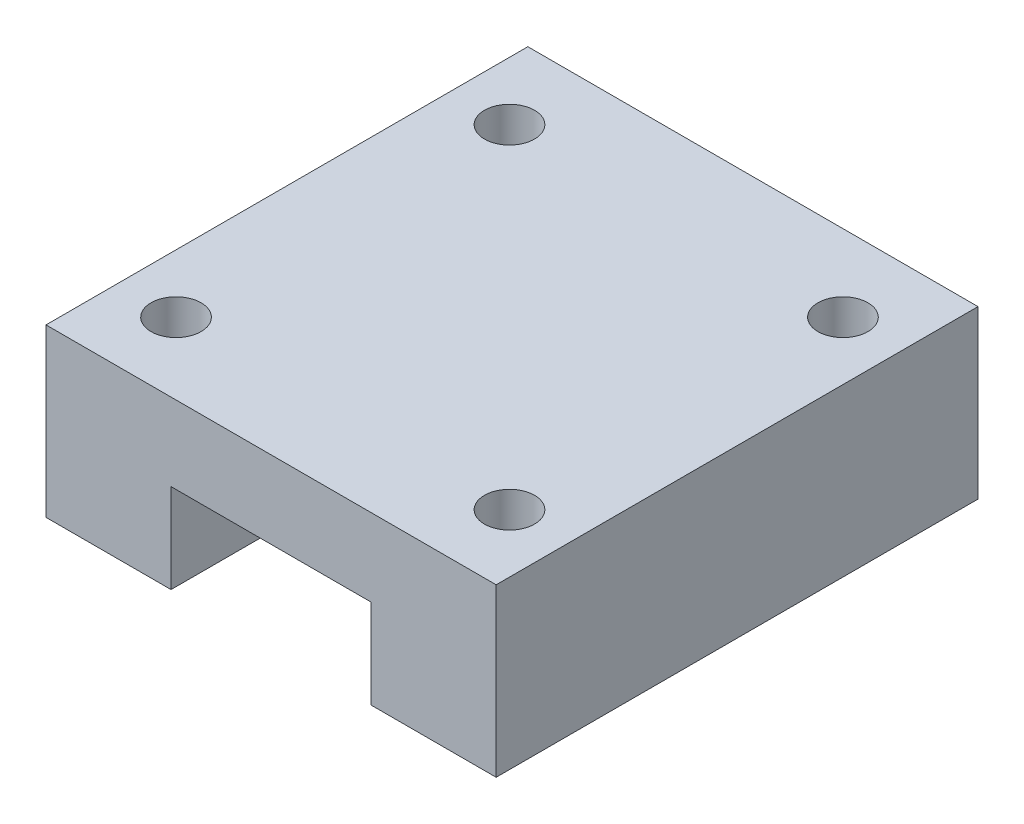
SolidWorks part; units mm, degrees
ref_plane "Front Plane" through (0, 0, 0) normal (0, 0, 1) x (1, 0, 0)
ref_plane "Top Plane" through (0, 0, 0) normal (0, 1, 0) x (1, 0, 0)
ref_plane "Right Plane" through (0, 0, 0) normal (1, 0, 0) x (0, 0, -1)
sketch "Sketch1" plane through (0, 0, 0) normal (0, 1, 0) x (1, 0, 0)
  line L1 (0, 0) -> (27, 0)
  line L2 (0, 0) -> (0, 28.9)
  line L3 (0, 28.9) -> (27, 28.9)
  line L4 (27, 0) -> (27, 28.9)
  dimension "D1" = 28.9
  dimension "D2" = 27
extrude "Boss-Extrude1" add sketch "Sketch1" along normal blind 10
sketch "Sketch2" plane through (0, 0, 0) normal (0, 0, 1) x (1, 0, 0)
  line L0 (0, 0) -> (27, 0) construction
  line L1 (7.5, 0) -> (19.5, 0)
  line L2 (7.5, 0) -> (7.5, 5.35)
  line L3 (7.5, 5.35) -> (19.5, 5.35)
  line L4 (19.5, 0) -> (19.5, 5.35)
  line L5 (0, 10) -> (0, 0) construction
  dimension "D1" = 5.35
  dimension "D2" = 12
  dimension "D3" = 7.5
extrude "Cut-Extrude1" cut sketch "Sketch2" against normal through all both and the other way through all
sketch "Sketch3" plane through (0, 10, 0) normal (0, 1, 0) x (1, 0, 0)
  line L0 (0, 28.9) -> (0, 0) construction
  line L1 (3.5, 4.3) -> (23.5, 4.3)
  line L2 (3.5, 4.3) -> (3.5, 24.3)
  line L3 (3.5, 24.3) -> (23.5, 24.3)
  line L4 (23.5, 4.3) -> (23.5, 24.3)
  line L5 (0, 0) -> (27, 0) construction
  dimension "D1" = 3.5
  dimension "D2" = 20
  dimension "D3" = 20
  dimension "D4" = 4.3
hole_wizard "Ø3.0mm Dowel Hole1" positions "Sketch6" profile "Sketch5" hole size "Ø3.0" standard "ANSI Metric"
sketch "Sketch6" plane through (0, 10, 0) normal (0, 1, 0) x (1, 0, 0)
  point P0 (3.5, 24.3)
  point P3 (23.5, 24.3)
  point P6 (3.5, 4.3)
  point P9 (23.5, 4.3)
sketch "Sketch5" plane through (3.5, 10, -24.3) normal (1, 0, 0) x (0, 0, 1)
  line L0 (0, 0) -> (0, 3.9013)
  line L1 (0, 3.9013) -> (1.5, 3)
  line L2 (1.5, 3) -> (1.5, 0)
  line L5 (1.5, 0) -> (0, 0)
  line L10 (0, 3.9013) -> (-1.5, 3) construction
  line L11 (0, -6.35) -> (0, 107.95) construction
  dimension "Hole Dia." = 3
  dimension "Hole Depth" = 3
  dimension "Drill Angle" = 118
